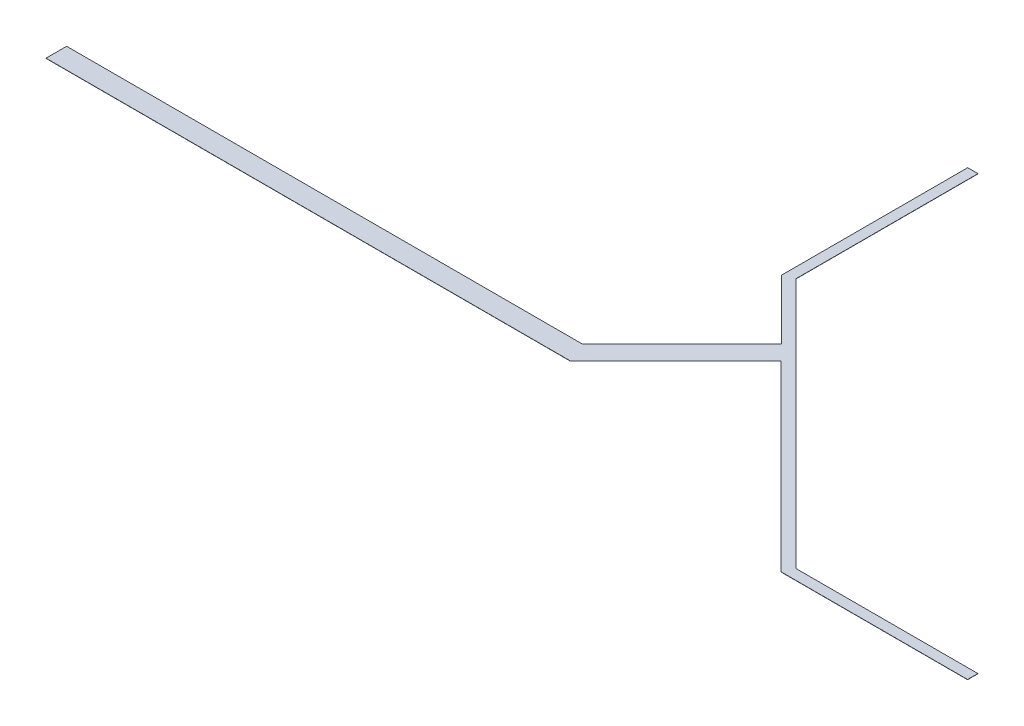
SolidWorks part; units mm, degrees
ref_plane "Front Plane" through (0, 0, 0) normal (0, 0, 1) x (1, 0, 0)
ref_plane "Top Plane" through (0, 0, 0) normal (0, 1, 0) x (1, 0, 0)
ref_plane "Right Plane" through (0, 0, 0) normal (1, 0, 0) x (0, 0, -1)
sketch "Sketch1" plane through (0, 0, 0) normal (0, 1, 0) x (1, 0, 0)
  line L0 (0, 0) -> (0, 2)
  line L1 (0, 0) -> (50.83, 0)
  line L2 (0, 2) -> (50, 2)
  line L3 (50, 2) -> (59.652, 11.652)
  line L4 (50.83, 0) -> (61.0618, 10.2318)
  line L5 (61.0618, 10.2318) -> (78.789, -7.4953)
  line L6 (59.652, 11.652) -> (53.8891, 17.4149)
  line L7 (78.789, -7.4953) -> (96.869, -7.4953)
  line L8 (53.8891, 17.4149) -> (53.8891, 35.4949)
  line L9 (53.8891, 35.4949) -> (54.8891, 35.4949)
  line L10 (96.869, -7.4953) -> (96.869, -6.4953)
  line L11 (96.869, -6.4953) -> (79.209, -6.4953)
  line L12 (54.8891, 35.4949) -> (54.8891, 17.8349)
  line L13 (54.8891, 17.8349) -> (79.209, -6.4953)
extrude "Boss-Extrude1" add sketch "Sketch1" along normal blind 0.02
